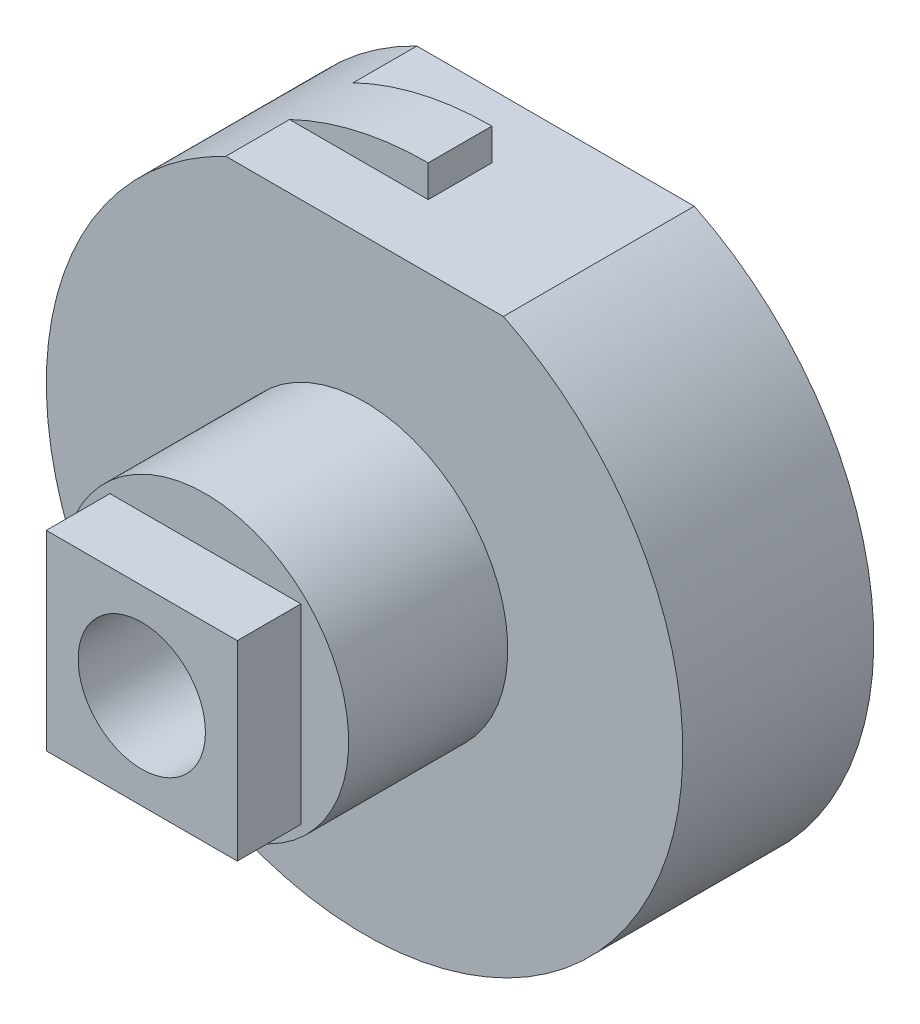
SolidWorks part; units mm, degrees
ref_plane "Alzado" through (0, 0, 0) normal (0, 0, 1) x (1, 0, 0)
ref_plane "Planta" through (0, 0, 0) normal (0, 1, 0) x (1, 0, 0)
ref_plane "Vista lateral" through (0, 0, 0) normal (1, 0, 0) x (0, 0, -1)
sketch "Croquis1" plane through (0, 0, 0) normal (0, 0, 1) x (1, 0, 0)
  line L0 (-0.75, 0.75) -> (0.75, -0.75) construction
  line L1 (-0.75, 0.75) -> (0.75, 0.75)
  line L2 (-0.75, 0.75) -> (-0.75, -0.75)
  line L3 (-0.75, -0.75) -> (0.75, -0.75)
  line L4 (0.75, 0.75) -> (0.75, -0.75)
  line L5 (-0.75, -0.75) -> (0.75, 0.75) construction
  point P4 (0, 0)
  dimension "D1" = 1.5
  dimension "D2" = 1.5
extrude "Saliente-Extruir1" add sketch "Croquis1" along normal blind 0.5
sketch "Croquis2" plane through (0, 0, 0) normal (0, 0, -1) x (-1, 0, 0)
  circle A0 centre (0, 0) radius 1.125
  dimension "D1" = 2.25
extrude "Saliente-Extruir2" add sketch "Croquis2" along normal blind 1.25
sketch "Croquis5" plane through (0, 0, -1.25) normal (0, 0, -1) x (-1, 0, 0)
  circle A0 centre (0, 0) radius 2.5
  dimension "D1" = 5
extrude "Saliente-Extruir5" add sketch "Croquis5" along normal blind 1.5
sketch "Croquis6" plane through (0, 0, -2.75) normal (0, 0, -1) x (-1, 0, 0)
  circle A0 centre (0, 0) radius 1.25
  dimension "D1" = 2.5
extrude "Saliente-Extruir6" add sketch "Croquis6" along normal blind 0.25
sketch "Croquis7" plane through (0, 0, -3) normal (0, 0, -1) x (-1, 0, 0)
  circle A0 centre (0, 0) radius 0.5
  dimension "D1" = 1
extrude "Saliente-Extruir7" add sketch "Croquis7" along normal blind 0.5
ref_plane "Plano1" through (0, 2.25, 0) normal (0, 1, 0) x (-1, 0, 0)
sketch "Croquis11" plane through (0, 2.25, 0) normal (0, 1, 0) x (-1, 0, 0)
  line L0 (2.5, -1.25) -> (-2.5, -1.25) construction
  line L1 (-1.5, -1.25) -> (1.5, -1.25)
  line L2 (-1.5, -1.25) -> (-1.5, -2.75)
  line L3 (-1.5, -2.75) -> (1.5, -2.75)
  line L4 (1.5, -1.25) -> (1.5, -1.75)
  line L5 (-2.5, -2.75) -> (2.5, -2.75) construction
  line L6 (1.5, -2.25) -> (1.5, -2.75)
  line L7 (1.5, -1.75) -> (0, -1.75)
  line L9 (1.5, -2.25) -> (0, -2.25)
  line L10 (0, -1.75) -> (0, -2.25)
  point P8 (0, -1.25)
  dimension "D1" = 3
  dimension "D3" = 0.5
  dimension "D4" = 0.5
extrude "Cortar-Extruir1" cut sketch "Croquis11" along normal blind 10
hole_wizard "Taladro roscado M1x0.251" positions "Croquis10" profile "Croquis9" tap size "M1x0.25" standard "KS"
sketch "Croquis10" plane through (0, 0, 0.5) normal (0, 0, 1) x (1, 0, 0)
  line L0 (0.75, 0.75) -> (-0.75, 0.75) construction
  line L1 (-0.75, 0.75) -> (-0.75, -0.75) construction
  point P0 (0, 0)
  point P4 (0, 0.75)
  point P7 (-0.75, 0)
sketch "Croquis9" plane through (0, 0, 0.5) normal (1, 0, 0) x (0, -1, 0)
  line L0 (0, 0) -> (0, 2.4753)
  line L1 (0, 2.4753) -> (0.375, 2.25)
  line L2 (0.375, 2.25) -> (0.375, 2)
  line L3 (0.375, 2) -> (0.5, 2)
  line L4 (0.5, 2) -> (0.5, 0)
  line L5 (0.5, 0) -> (0, 0)
  line L10 (0, 2.4753) -> (-0.375, 2.25) construction
  line L11 (0, -6.35) -> (0, 107.95) construction
  dimension "Diámetro de perforador para roscar" = 0.75
  dimension "Profundidad de perforador para roscar" = 2.25
  dimension "Diámetro mayor de rosca" = 1
  dimension "Profundidad de rosca" = 2
  dimension "Ángulo de perforador" = 118
